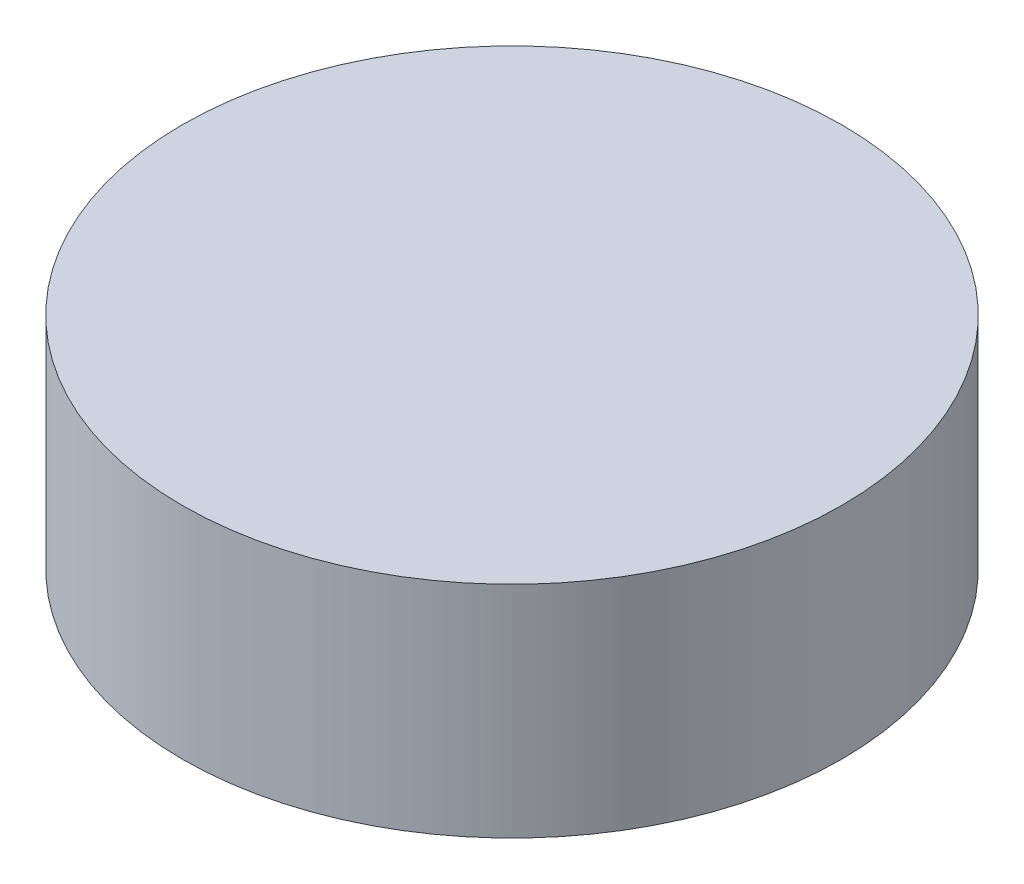
SolidWorks part; units mm, degrees
ref_plane "Front Plane" through (0, 0, 0) normal (0, 0, 1) x (1, 0, 0)
ref_plane "Top Plane" through (0, 0, 0) normal (0, 1, 0) x (1, 0, 0)
ref_plane "Right Plane" through (0, 0, 0) normal (1, 0, 0) x (0, 0, -1)
sketch "Sketch1" plane through (0, 0, 0) normal (0, 1, 0) x (1, 0, 0)
  circle A0 centre (0, 0) radius 15
  dimension "D1" = 30
extrude "Boss-Extrude1" add sketch "Sketch1" along normal blind 10
sketch "Sketch2" plane through (0, 0, 0) normal (0, -1, 0) x (1, 0, 0)
  circle A0 centre (0, 0) radius 4.5
  dimension "D1" = 9
extrude "Boss-Extrude2" add sketch "Sketch2" along normal blind 3
